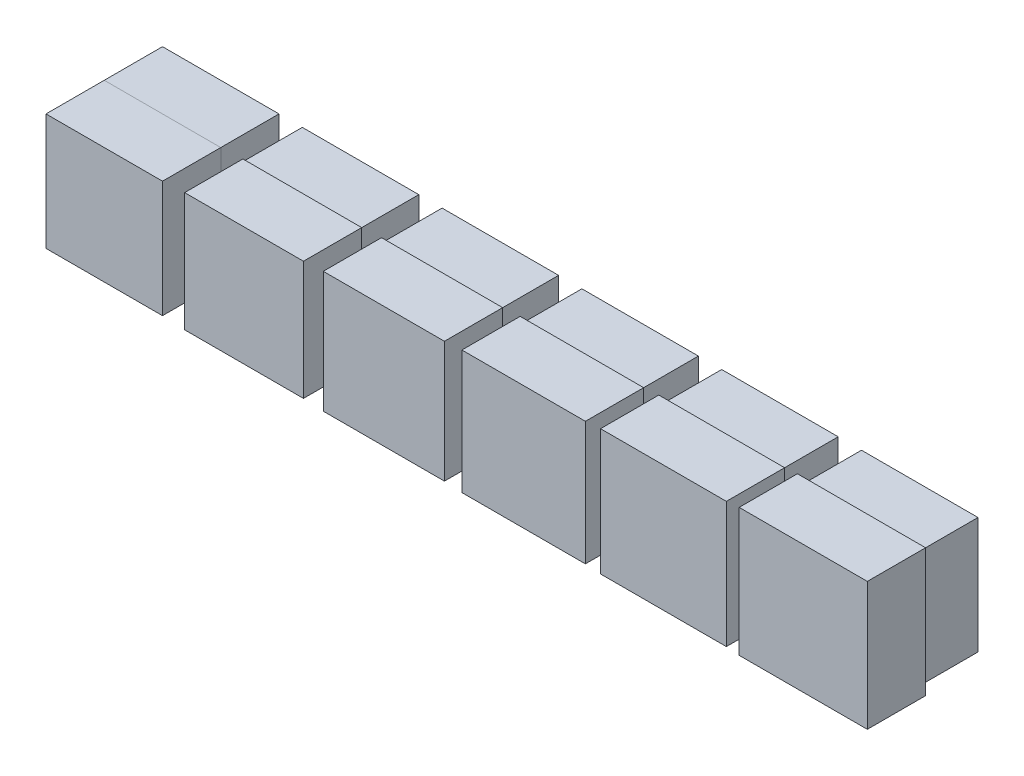
SolidWorks part; units mm, degrees
ref_plane "Front Plane" through (0, 0, 0) normal (0, 0, 1) x (1, 0, 0)
ref_plane "Top Plane" through (0, 0, 0) normal (0, 1, 0) x (1, 0, 0)
ref_plane "Right Plane" through (0, 0, 0) normal (1, 0, 0) x (0, 0, -1)
sketch "Sketch1" plane through (0, 0, 0) normal (0, 0, 1) x (1, 0, 0)
  line L0 (0, 0) -> (122.664, 0) construction
  line L1 (5, -5) -> (-5, -5)
  line L2 (5, -5) -> (5, 5)
  line L3 (5, 5) -> (-5, 5)
  line L4 (-5, -5) -> (-5, 5)
  line L5 (5, -5) -> (-5, 5) construction
  line L6 (5, 5) -> (-5, -5) construction
  line L8 (17, -5) -> (7, -5)
  line L9 (17, -5) -> (17, 5)
  line L10 (17, 5) -> (7, 5)
  line L11 (7, -5) -> (7, 5)
  line L12 (17, -5) -> (7, 5) construction
  line L13 (17, 5) -> (7, -5) construction
  line L14 (29, -5) -> (19, -5)
  line L15 (29, -5) -> (29, 5)
  line L16 (29, 5) -> (19, 5)
  line L17 (19, -5) -> (19, 5)
  line L18 (29, -5) -> (19, 5) construction
  line L19 (29, 5) -> (19, -5) construction
  line L20 (41, -5) -> (31, -5)
  line L21 (41, -5) -> (41, 5)
  line L22 (41, 5) -> (31, 5)
  line L23 (31, -5) -> (31, 5)
  line L24 (41, -5) -> (31, 5) construction
  line L25 (41, 5) -> (31, -5) construction
  line L26 (53, -5) -> (43, -5)
  line L27 (53, -5) -> (53, 5)
  line L28 (53, 5) -> (43, 5)
  line L29 (43, -5) -> (43, 5)
  line L30 (53, -5) -> (43, 5) construction
  line L31 (53, 5) -> (43, -5) construction
  line L32 (65, -5) -> (55, -5)
  line L33 (65, -5) -> (65, 5)
  line L34 (65, 5) -> (55, 5)
  line L35 (55, -5) -> (55, 5)
  line L36 (65, -5) -> (55, 5) construction
  line L37 (65, 5) -> (55, -5) construction
  point P0 (0, 0)
  point P8 (12, 0)
  point P13 (24, 0)
  point P18 (36, 0)
  point P23 (48, 0)
  point P28 (60, 0)
  dimension "D1" = 10
  dimension "D2" = 10
  dimension "D3" = 10
  dimension "D4" = 10
  dimension "D5" = 10
  dimension "D6" = 10
  dimension "D7" = 10
  dimension "D8" = 12
  dimension "D9" = 12
  dimension "D10" = 12
  dimension "D11" = 12
  dimension "D12" = 12
extrude "Boss-Extrude1" add sketch "Sketch1" along normal blind 5
sketch "Sketch2" plane through (0, 0, 5) normal (0, 0, 1) x (1, 0, 0)
  line L0 (-5, 5) -> (-5, -5) construction
  line L1 (5, -5) -> (-5, -5)
  line L2 (5, -5) -> (5, 5)
  line L3 (5, 5) -> (-5, 5)
  line L4 (-5, -5) -> (-5, 5)
  line L5 (5, -5) -> (-5, 5) construction
  line L6 (5, 5) -> (-5, -5) construction
  line L7 (5, 5) -> (-5, 5) construction
  line L8 (0, 0) -> (73.5386, 0) construction
  line L9 (7, 5) -> (7, -5) construction
  line L10 (7, -5) -> (17, -5) construction
  line L11 (17, -5) -> (17, 5) construction
  line L12 (17, 5) -> (7, 5) construction
  line L13 (19, 5) -> (19, -5) construction
  line L14 (19, -5) -> (29, -5) construction
  line L15 (29, -5) -> (29, 5) construction
  line L16 (29, 5) -> (19, 5) construction
  line L17 (31, 5) -> (31, -5) construction
  line L18 (31, -5) -> (41, -5) construction
  line L19 (41, -5) -> (41, 5) construction
  line L20 (41, 5) -> (31, 5) construction
  line L21 (43, 5) -> (43, -5) construction
  line L22 (43, -5) -> (53, -5) construction
  line L23 (53, -5) -> (53, 5) construction
  line L24 (53, 5) -> (43, 5) construction
  line L25 (55, 5) -> (55, -5) construction
  line L26 (55, -5) -> (65, -5) construction
  line L27 (65, -5) -> (65, 5) construction
  line L28 (65, 5) -> (55, 5) construction
  line L29 (7, 5) -> (7, -5) construction
  line L30 (7, -5) -> (17, -5) construction
  line L31 (17, -5) -> (17, 5) construction
  line L32 (17, 5) -> (7, 5) construction
  line L33 (19, 5) -> (19, -5) construction
  line L34 (19, -5) -> (29, -5) construction
  line L35 (29, -5) -> (29, 5) construction
  line L36 (29, 5) -> (19, 5) construction
  line L37 (31, 5) -> (31, -5) construction
  line L38 (31, -5) -> (41, -5) construction
  line L39 (41, -5) -> (41, 5) construction
  line L40 (41, 5) -> (31, 5) construction
  line L41 (43, 5) -> (43, -5) construction
  line L42 (43, -5) -> (53, -5) construction
  line L43 (53, -5) -> (53, 5) construction
  line L44 (53, 5) -> (43, 5) construction
  line L45 (55, 5) -> (55, -5) construction
  line L46 (55, -5) -> (65, -5) construction
  line L47 (65, -5) -> (65, 5) construction
  line L48 (65, 5) -> (55, 5) construction
  line L50 (17.1, -5.1) -> (6.9, -5.1)
  line L51 (17.1, -5.1) -> (17.1, 5.1)
  line L52 (17.1, 5.1) -> (6.9, 5.1)
  line L53 (6.9, -5.1) -> (6.9, 5.1)
  line L54 (17.1, -5.1) -> (6.9, 5.1) construction
  line L55 (17.1, 5.1) -> (6.9, -5.1) construction
  line L56 (29.2, -5.2) -> (18.8, -5.2)
  line L57 (29.2, -5.2) -> (29.2, 5.2)
  line L58 (29.2, 5.2) -> (18.8, 5.2)
  line L59 (18.8, -5.2) -> (18.8, 5.2)
  line L60 (29.2, -5.2) -> (18.8, 5.2) construction
  line L61 (29.2, 5.2) -> (18.8, -5.2) construction
  line L62 (41.3, -5.3) -> (30.7, -5.3)
  line L63 (41.3, -5.3) -> (41.3, 5.3)
  line L64 (41.3, 5.3) -> (30.7, 5.3)
  line L65 (30.7, -5.3) -> (30.7, 5.3)
  line L66 (41.3, -5.3) -> (30.7, 5.3) construction
  line L67 (41.3, 5.3) -> (30.7, -5.3) construction
  line L68 (53.4, -5.4) -> (42.6, -5.4)
  line L69 (53.4, -5.4) -> (53.4, 5.4)
  line L70 (53.4, 5.4) -> (42.6, 5.4)
  line L71 (42.6, -5.4) -> (42.6, 5.4)
  line L72 (53.4, -5.4) -> (42.6, 5.4) construction
  line L73 (53.4, 5.4) -> (42.6, -5.4) construction
  line L74 (65.5, -5.5) -> (54.5, -5.5)
  line L75 (65.5, -5.5) -> (65.5, 5.5)
  line L76 (65.5, 5.5) -> (54.5, 5.5)
  line L77 (54.5, -5.5) -> (54.5, 5.5)
  line L78 (65.5, -5.5) -> (54.5, 5.5) construction
  line L79 (65.5, 5.5) -> (54.5, -5.5) construction
  point P0 (0, 0)
  point P30 (12, 0)
  point P37 (24, 0)
  point P42 (36, 0)
  point P47 (48, 0)
  point P52 (60, 0)
  dimension "D1" = 10.2
  dimension "D2" = 10.2
  dimension "D3" = 10.4
  dimension "D4" = 10.4
  dimension "D5" = 10.6
  dimension "D6" = 10.6
  dimension "D7" = 10.8
  dimension "D8" = 10.8
  dimension "D9" = 11
  dimension "D10" = 11
extrude "Boss-Extrude2" add sketch "Sketch2" along normal blind 5 separate body
